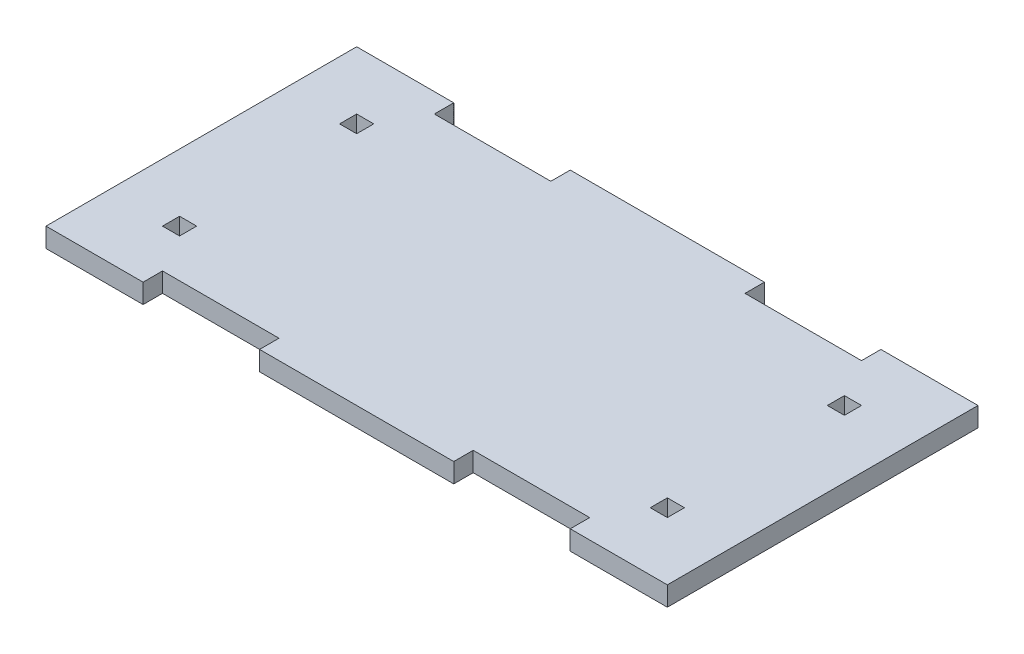
SolidWorks part; units mm, degrees
ref_plane "Front Plane" through (0, 0, 0) normal (0, 0, 1) x (1, 0, 0)
ref_plane "Top Plane" through (0, 0, 0) normal (0, 1, 0) x (1, 0, 0)
ref_plane "Right Plane" through (0, 0, 0) normal (1, 0, 0) x (0, 0, -1)
sketch "Sketch1" plane through (0, 0, 0) normal (0, 1, 0) x (1, 0, 0)
  line L1 (-101.6, -50.8) -> (101.6, -50.8)
  line L2 (-101.6, -50.8) -> (-101.6, 50.8)
  line L3 (-101.6, 50.8) -> (101.6, 50.8)
  line L4 (101.6, -50.8) -> (101.6, 50.8)
  line L5 (-101.6, -50.8) -> (101.6, 50.8) construction
  line L6 (-101.6, 50.8) -> (101.6, -50.8) construction
  line L7 (-69.85, -50.8) -> (-31.75, -50.8)
  line L8 (-69.85, -50.8) -> (-69.85, -44.45)
  line L9 (-69.85, -44.45) -> (-31.75, -44.45)
  line L10 (-31.75, -50.8) -> (-31.75, -44.45)
  line L11 (31.75, -50.8) -> (69.85, -50.8)
  line L12 (31.75, -50.8) -> (31.75, -44.45)
  line L13 (31.75, -44.45) -> (69.85, -44.45)
  line L14 (69.85, -50.8) -> (69.85, -44.45)
  line L15 (69.85, 50.8) -> (31.75, 50.8)
  line L16 (69.85, 50.8) -> (69.85, 44.45)
  line L17 (69.85, 44.45) -> (31.75, 44.45)
  line L18 (31.75, 50.8) -> (31.75, 44.45)
  line L19 (-31.75, 50.8) -> (-69.85, 50.8)
  line L20 (-31.75, 50.8) -> (-31.75, 44.45)
  line L21 (-31.75, 44.45) -> (-69.85, 44.45)
  line L22 (-69.85, 50.8) -> (-69.85, 44.45)
  line L23 (-82.55, -26.162) -> (-76.962, -26.162)
  line L24 (-82.55, -26.162) -> (-82.55, -31.75)
  line L25 (-82.55, -31.75) -> (-76.962, -31.75)
  line L26 (-76.962, -26.162) -> (-76.962, -31.75)
  line L27 (-82.55, 31.75) -> (-76.962, 31.75)
  line L28 (-82.55, 31.75) -> (-82.55, 26.162)
  line L29 (-82.55, 26.162) -> (-76.962, 26.162)
  line L30 (-76.962, 31.75) -> (-76.962, 26.162)
  line L31 (76.962, 31.75) -> (82.55, 31.75)
  line L32 (76.962, 31.75) -> (76.962, 26.162)
  line L33 (76.962, 26.162) -> (82.55, 26.162)
  line L34 (82.55, 31.75) -> (82.55, 26.162)
  line L35 (82.55, -31.75) -> (76.962, -31.75)
  line L36 (82.55, -31.75) -> (82.55, -26.162)
  line L37 (82.55, -26.162) -> (76.962, -26.162)
  line L38 (76.962, -31.75) -> (76.962, -26.162)
  point P0 (0, 0)
  dimension "D1" = 101.6
  dimension "D2" = 203.2
  dimension "D3" = 38.1
  dimension "D4" = 38.1
  dimension "D5" = 31.75
  dimension "D6" = 31.75
  dimension "D7" = 6.35
  dimension "D8" = 6.35
  dimension "D9" = 5.588
  dimension "D10" = 5.588
  dimension "D11" = 19.05
  dimension "D12" = 19.05
  dimension "D13" = 5.588
  dimension "D14" = 5.588
  dimension "D15" = 19.05
  dimension "D16" = 19.05
extrude "Boss-Extrude1" add sketch "Sketch1" along normal blind 6.35 contours L22 L3 L2 L1 L8 L9 L10 L12 L13 L14 L4 L16 L17 L18 L20 L21
